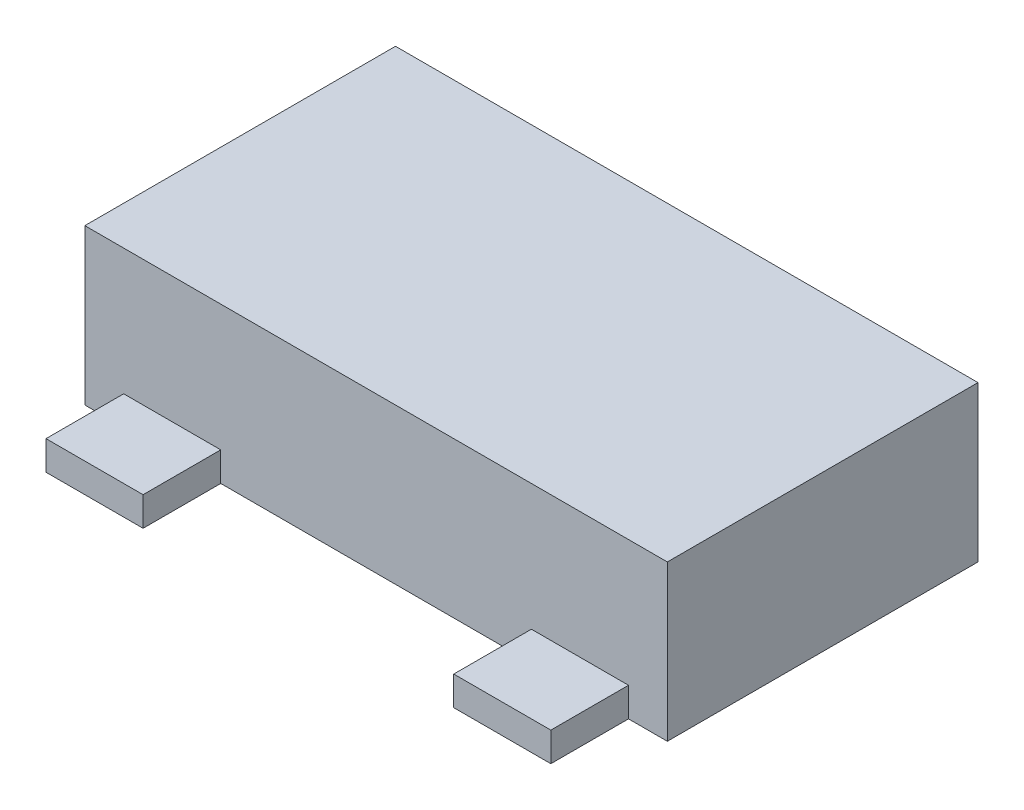
SolidWorks part; units mm, degrees
ref_plane "Front Plane" through (0, 0, 0) normal (0, 0, 1) x (1, 0, 0)
ref_plane "Top Plane" through (0, 0, 0) normal (0, 1, 0) x (1, 0, 0)
ref_plane "Right Plane" through (0, 0, 0) normal (1, 0, 0) x (0, 0, -1)
sketch "BaseS" plane through (0, 0, 0) normal (0, 1, 0) x (1, 0, 0)
  line L1 (-1.5, 0.8) -> (1.5, 0.8)
  line L2 (-1.5, 0.8) -> (-1.5, -0.8)
  line L3 (-1.5, -0.8) -> (1.5, -0.8)
  line L4 (1.5, 0.8) -> (1.5, -0.8)
  line L5 (-1.5, 0.8) -> (1.5, -0.8) construction
  line L6 (-1.5, -0.8) -> (1.5, 0.8) construction
  point P0 (0, 0)
  dimension "Width" = 3
  dimension "Length" = 1.6
extrude "Base" add sketch "BaseS" along normal blind 0.8
sketch "LegS" plane through (0, 0, 0) normal (0, 1, 0) x (1, 0, 0)
  line L0 (1.5, 0.8) -> (-1.5, 0.8) construction
  line L1 (-0.25, 0.8) -> (0.25, 0.8)
  line L2 (-0.25, 0.8) -> (-0.25, 1.2)
  line L3 (-0.25, 1.2) -> (0.25, 1.2)
  line L4 (0.25, 0.8) -> (0.25, 1.2)
  point P6 (0, 0.8)
  dimension "Length" = 0.4
  dimension "Width" = 0.5
extrude "Leg" add sketch "LegS" along normal blind 0.15
sketch "SideLegS" plane through (0, 0, 0) normal (0, 1, 0) x (1, 0, 0)
  line L0 (-1.5, -0.8) -> (1.5, -0.8) construction
  line L1 (-1.3, -0.8) -> (-0.8, -0.8)
  line L2 (-1.3, -0.8) -> (-1.3, -1.2)
  line L3 (-1.3, -1.2) -> (-0.8, -1.2)
  line L4 (-0.8, -0.8) -> (-0.8, -1.2)
  line L5 (-0.25, 0.8) -> (-0.25, 1.2) construction
  line L6 (-0.25, 0.8) -> (0.25, 0.8) construction
  line L7 (-1.5, 0.8) -> (-1.5, -0.8) construction
  dimension "D1" = 0.2
extrude "SideLeg" add sketch "SideLegS" along normal up to surface (0.15 mm away) up to face at (0, 0.15, -1)
mirror "SLHM" about plane through (0, 0, 0) normal (1, 0, 0) of "SideLeg"
